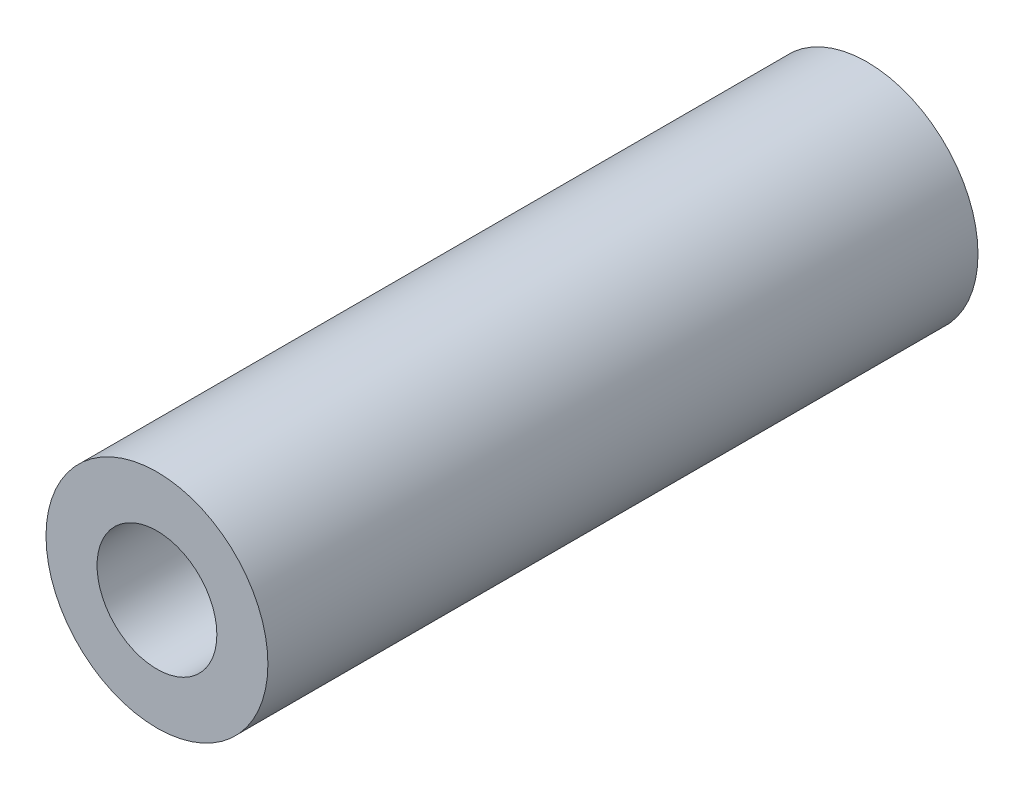
SolidWorks part; units mm, degrees
ref_plane "Front Plane" through (0, 0, 0) normal (0, 0, 1) x (1, 0, 0)
ref_plane "Top Plane" through (0, 0, 0) normal (0, 1, 0) x (1, 0, 0)
ref_plane "Right Plane" through (0, 0, 0) normal (1, 0, 0) x (0, 0, -1)
sketch "Esquisse1" plane through (0, 0, 0) normal (0, 0, 1) x (1, 0, 0)
  circle A0 centre (0, 0) radius 1.35
  circle A1 centre (0, 0) radius 2.5
  dimension "D1" = 2.7
  dimension "D2" = 5
extrude "Boss.-Extru.1" add sketch "Esquisse1" along normal blind 16
